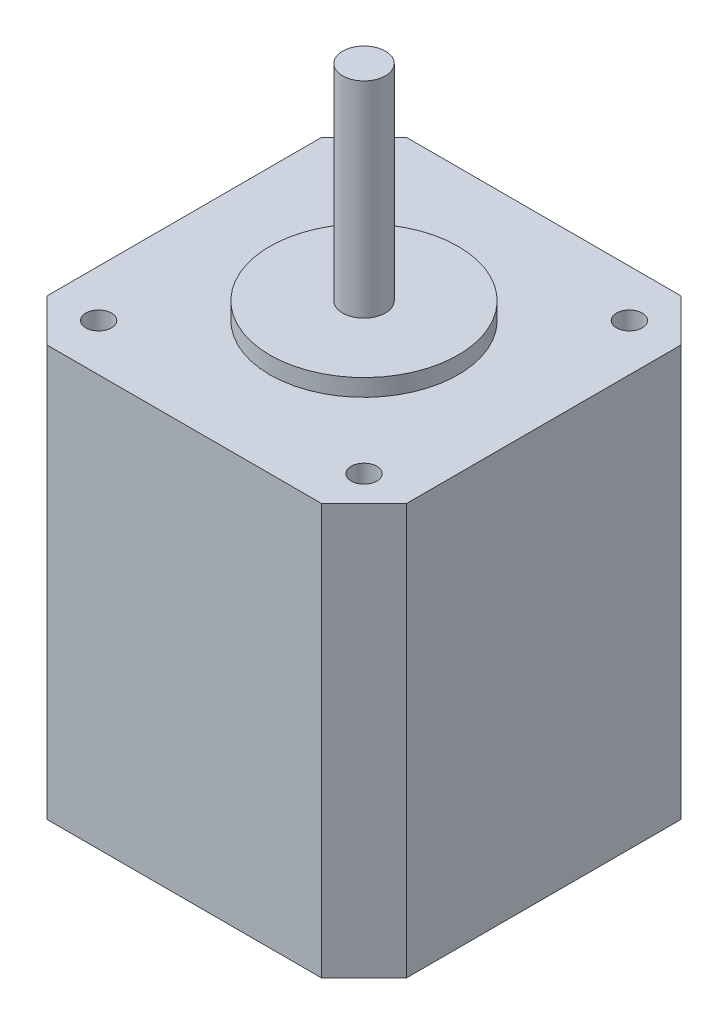
SolidWorks part; units mm, degrees
ref_plane "Front Plane" through (0, 0, 0) normal (0, 0, 1) x (1, 0, 0)
ref_plane "Top Plane" through (0, 0, 0) normal (0, 1, 0) x (1, 0, 0)
ref_plane "Right Plane" through (0, 0, 0) normal (1, 0, 0) x (0, 0, -1)
sketch "Sketch1" plane through (0, 0, 0) normal (0, 1, 0) x (1, 0, 0)
  line L1 (0, 0) -> (42, 0)
  line L2 (0, 0) -> (0, 42)
  line L3 (0, 42) -> (42, 42)
  line L4 (42, 0) -> (42, 42)
  line L5 (0, 0) -> (42, 42) construction
  line L6 (0, 42) -> (42, 0) construction
  point P4 (21, 21)
  dimension "D1" = 42
  dimension "D2" = 42
extrude "Boss-Extrude1" add sketch "Sketch1" along normal blind 48
sketch "Sketch5" plane through (0, 48, 0) normal (0, 1, 0) x (1, 0, 0)
  line L0 (42, 21) -> (0, 21) construction
  line L1 (42, 0) -> (42, 42) construction
  line L2 (0, 42) -> (0, 0) construction
  line L3 (21, 0) -> (21, 42) construction
  line L4 (0, 0) -> (42, 0) construction
  line L5 (42, 42) -> (0, 42) construction
  circle A0 centre (21, 21) radius 11
  dimension "D1" = 22
extrude "Boss-Extrude4" add sketch "Sketch5" along normal blind 2
sketch "Sketch6" plane through (0, 50, 0) normal (0, 1, 0) x (1, 0, 0)
  circle A0 centre (21, 21) radius 2.5
  dimension "D1" = 5
extrude "Boss-Extrude5" add sketch "Sketch6" along normal blind 24
sketch "Sketch8" plane through (0, 48, 0) normal (0, 1, 0) x (1, 0, 0)
  line L0 (36.5, 42) -> (36.5, 0) construction
  line L1 (42, 42) -> (0, 42) construction
  line L2 (0, 0) -> (42, 0) construction
  line L3 (42, 5.5) -> (0, 5.5) construction
  line L4 (42, 0) -> (42, 42) construction
  line L5 (0, 42) -> (0, 0) construction
  line L6 (42, 21) -> (0, 21) construction
  line L7 (21, 42) -> (21, 0) construction
  circle A0 centre (36.5, 5.5) radius 1.5
  circle A1 centre (36.5, 36.5) radius 1.5
  circle A2 centre (5.5, 5.5) radius 1.5
  circle A3 centre (5.5, 36.5) radius 1.5
  dimension "D3" = 3
  dimension "D1" = 15.5
  dimension "D2" = 15.5
extrude "Cut-Extrude1" cut sketch "Sketch8" against normal blind 4.5
sketch "Sketch9" plane through (0, 48, 0) normal (0, 1, 0) x (1, 0, 0)
  line L0 (0, 4.9497) -> (4.9497, 0)
  line L1 (0, 42) -> (0, 0) construction
  line L2 (0, 0) -> (42, 0) construction
  line L3 (37.0503, 0) -> (42, 4.9497)
  line L4 (42, 0) -> (42, 42) construction
  line L5 (37.0503, 42) -> (42, 37.0503)
  line L6 (42, 42) -> (0, 42) construction
  line L7 (0, 37.0503) -> (4.9497, 42)
  line L8 (4.9497, 42) -> (0, 42)
  line L9 (0, 42) -> (0, 37.0503)
  line L10 (0, 4.9497) -> (0, 0)
  line L11 (0, 0) -> (4.9497, 0)
  line L12 (42, 4.9497) -> (42, 0)
  line L13 (42, 0) -> (37.0503, 0)
  line L14 (42, 37.0503) -> (42, 42)
  line L15 (42, 42) -> (37.0503, 42)
  dimension "D1" = 7
  dimension "D2" = 7
  dimension "D3" = 7
  dimension "D4" = 7
extrude "Cut-Extrude2" cut sketch "Sketch9" against normal through all
